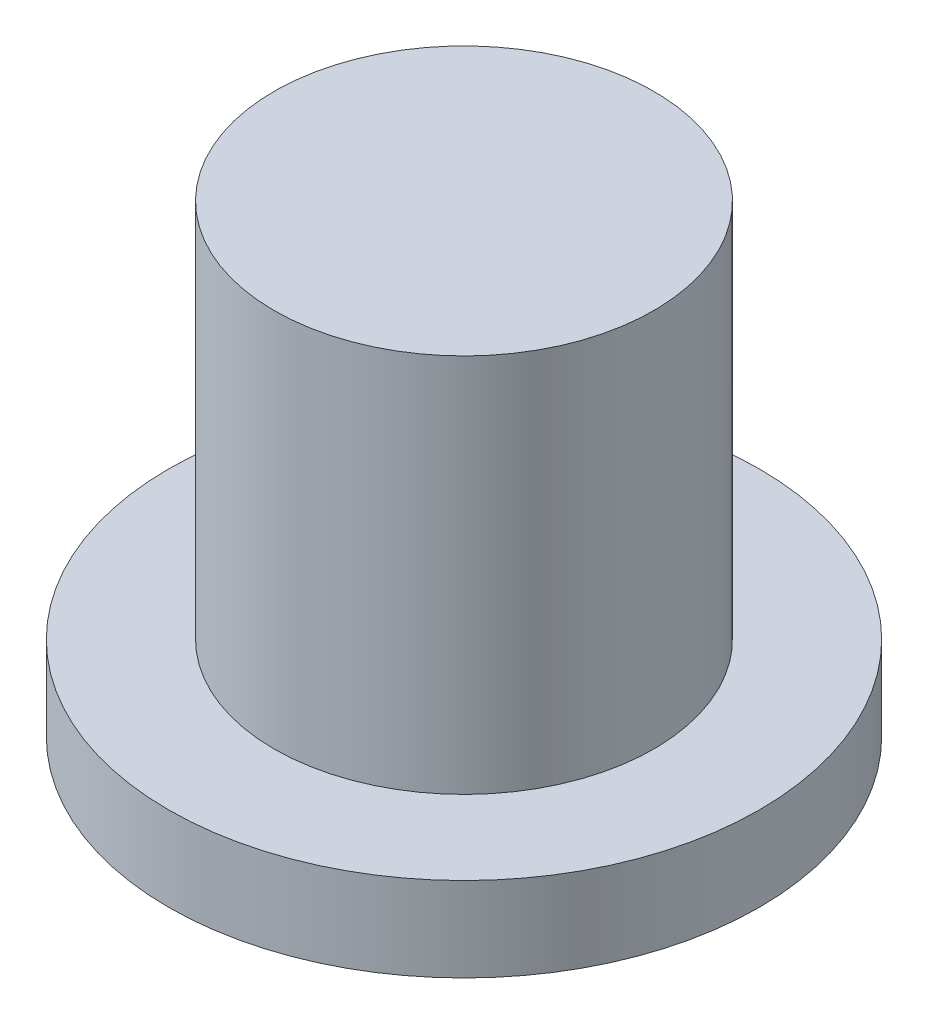
SolidWorks part; units mm, degrees
ref_plane "Спереди" through (0, 0, 0) normal (0, 0, 1) x (1, 0, 0)
ref_plane "Сверху" through (0, 0, 0) normal (0, 1, 0) x (1, 0, 0)
ref_plane "Справа" through (0, 0, 0) normal (1, 0, 0) x (0, 0, -1)
sketch "Эскиз1" plane through (0, 0, 0) normal (0, 1, 0) x (1, 0, 0)
  circle A0 centre (0, 0) radius 3.5
  dimension "D1" = 7
extrude "Бобышка-Вытянуть1" add sketch "Эскиз1" along normal blind 1
sketch "Эскиз2" plane through (0, 1, 0) normal (0, 1, 0) x (1, 0, 0)
  circle A0 centre (0, 0) radius 2.25
  dimension "D1" = 4.5
extrude "Бобышка-Вытянуть2" add sketch "Эскиз2" along normal blind 4.5
